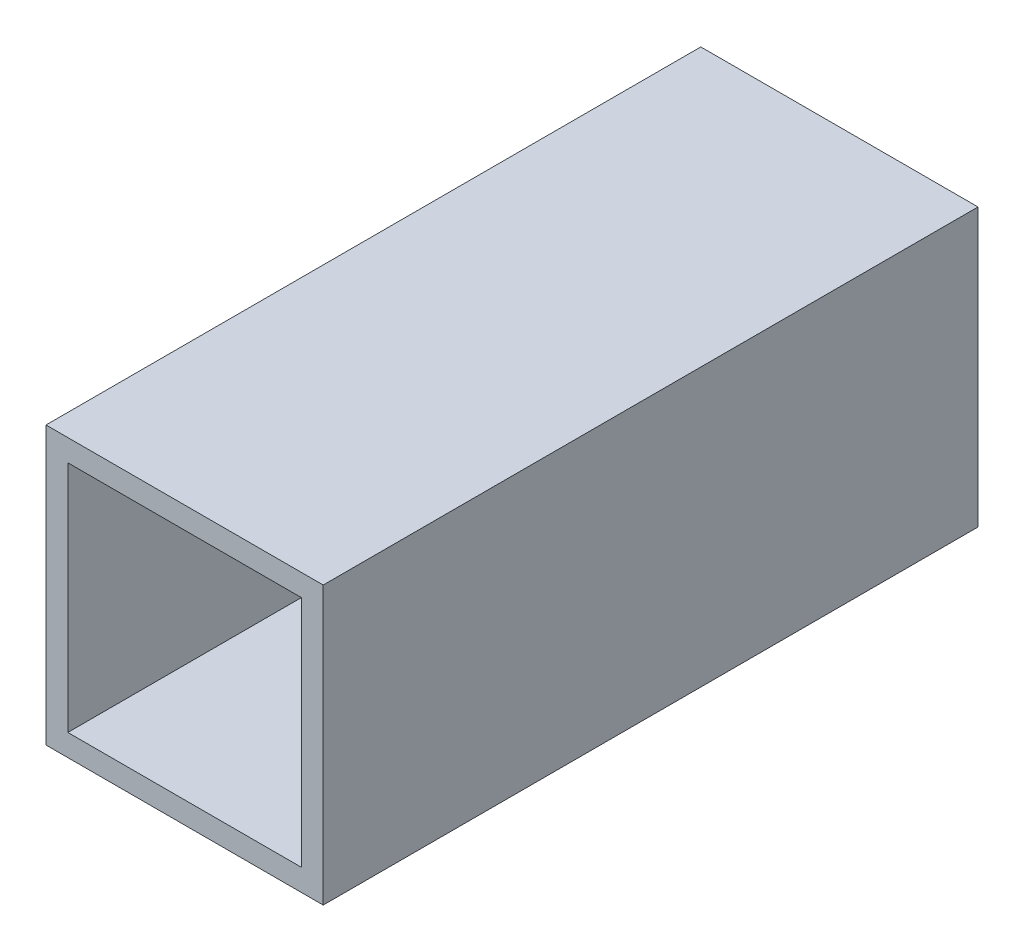
SolidWorks part; units mm, degrees
ref_plane "Front Plane" through (0, 0, 0) normal (0, 0, 1) x (1, 0, 0)
ref_plane "Top Plane" through (0, 0, 0) normal (0, 1, 0) x (1, 0, 0)
ref_plane "Right Plane" through (0, 0, 0) normal (1, 0, 0) x (0, 0, -1)
sketch "Sketch1" plane through (0, 0, 0) normal (0, 0, 1) x (1, 0, 0)
  line L0 (10.7, 10.7) -> (-10.7, 10.7)
  line L1 (12.7, 12.7) -> (-12.7, 12.7)
  line L2 (12.7, 12.7) -> (12.7, -12.7)
  line L3 (12.7, -12.7) -> (-12.7, -12.7)
  line L4 (-12.7, 12.7) -> (-12.7, -12.7)
  line L5 (12.7, 12.7) -> (-12.7, -12.7) construction
  line L6 (12.7, -12.7) -> (-12.7, 12.7) construction
  line L7 (-10.7, 10.7) -> (-10.7, -10.7)
  line L8 (10.7, -10.7) -> (-10.7, -10.7)
  line L9 (10.7, 10.7) -> (10.7, -10.7)
  point P0 (0, 0)
  dimension "D1" = 25.4
  dimension "D2" = 2
extrude "Boss-Extrude1" add sketch "Sketch1" along normal blind 60
